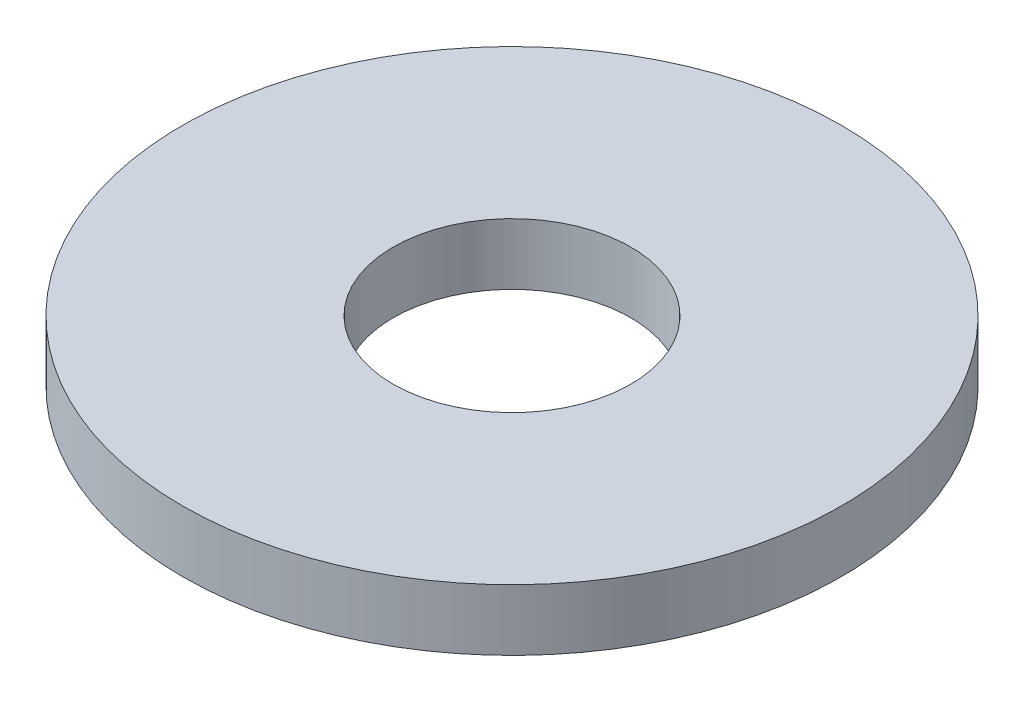
SolidWorks part; units mm, degrees
ref_plane "Front Plane" through (0, 0, 0) normal (0, 0, 1) x (1, 0, 0)
ref_plane "Top Plane" through (0, 0, 0) normal (0, 1, 0) x (1, 0, 0)
ref_plane "Right Plane" through (0, 0, 0) normal (1, 0, 0) x (0, 0, -1)
sketch "Sketch1" plane through (0, 0, 0) normal (0, 1, 0) x (1, 0, 0)
  circle A0 centre (0, 0) radius 3.2
  circle A1 centre (0, 0) radius 8.875
  dimension "D1" = 6.4
  dimension "D2" = 17.75
extrude "Boss-Extrude1" add sketch "Sketch1" along normal blind 1.65
